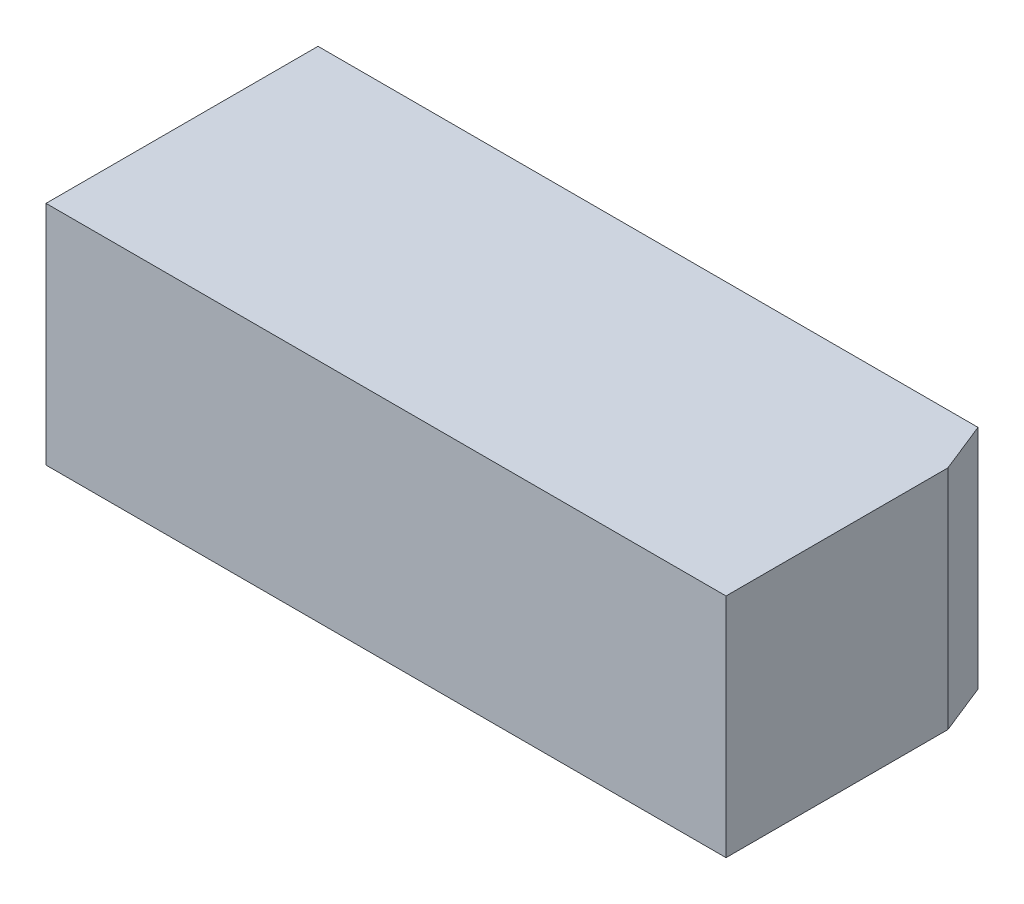
SolidWorks part; units mm, degrees
ref_plane "Front Plane" through (0, 0, 0) normal (0, 0, 1) x (1, 0, 0)
ref_plane "Top Plane" through (0, 0, 0) normal (0, 1, 0) x (1, 0, 0)
ref_plane "Right Plane" through (0, 0, 0) normal (1, 0, 0) x (0, 0, -1)
sketch "Sketch1" plane through (0, 0, 0) normal (0, 1, 0) x (1, 0, 0)
  line L1 (7.5, 3) -> (-7.5, 3)
  line L2 (7.5, 3) -> (7.5, -3)
  line L3 (7.5, -3) -> (-7.5, -3)
  line L4 (-7.5, 3) -> (-7.5, -3)
  line L5 (7.5, 3) -> (-7.5, -3) construction
  line L6 (7.5, -3) -> (-7.5, 3) construction
  point P0 (0, 0)
  dimension "D1" = 6
  dimension "D2" = 15
extrude "Main Body" add sketch "Sketch1" along normal blind 5
sketch "Sketch3" plane through (0, 0, 0) normal (0, -1, 0) x (1, 0, 0)
  line L0 (-7.5, -3) -> (-7.5, 3) construction
  line L1 (0, 0) -> (-4.5, 0) construction
  circle A0 centre (-4.5, 0) radius 1.25
  dimension "D1" = 2.5
  dimension "D2" = 3
extrude "GRIN Hole" cut sketch "Sketch3" against normal blind 4
sketch "Sketch2" plane through (0, 0, 0) normal (0, -1, 0) x (1, 0, 0)
  line L0 (-6.25, 1.875) -> (-6.25, -1.875) construction
  line L1 (-1.5, 0) -> (-4.5, 0) construction
  line L2 (-4.5, 0) -> (-6.25, 0) construction
  circle A0 centre (-6.25, -1.875) radius 0.795
  circle A1 centre (-6.25, 1.875) radius 0.795
  circle A2 centre (-1.5, 0) radius 0.795
  circle A3 centre (-4.5, 0) radius 1.25 construction
  dimension "D4" = 1.59
  dimension "D1" = 3.75
  dimension "D2" = 3
  dimension "D3" = 1.75
extrude "Magnet Holes" cut sketch "Sketch2" against normal blind 1
sketch "Sketch4" plane through (0, 0, 0) normal (0, -1, 0) x (1, 0, 0)
  line L0 (-7.5, 3) -> (7.5, -3) construction
  line L1 (7.5, 3) -> (7.5, -3) construction
  line L4 (7.5, -3) -> (-7.5, -3) construction
  line L5 (7.058, -3) -> (7.5, -1.8951)
  line L6 (7.5, -1.8951) -> (7.5, -3)
  line L7 (7.5, -3) -> (7.058, -3)
  dimension "D1" = 1.19
extrude "Set Screw Indent" cut sketch "Sketch4" against normal through all
sketch "Sketch5" plane through (0, 0, 0) normal (0, -1, 0) x (1, 0, 0)
  line L0 (7.058, -3) -> (-7.5, -3) construction
  line L1 (-7.5, -3) -> (-7.5, 3) construction
  circle A0 centre (-2, -2) radius 0.5
  dimension "D1" = 1
  dimension "D2" = 1
  dimension "D3" = 5.5
extrude "Cut-Extrude1" cut sketch "Sketch5" against normal blind 2
